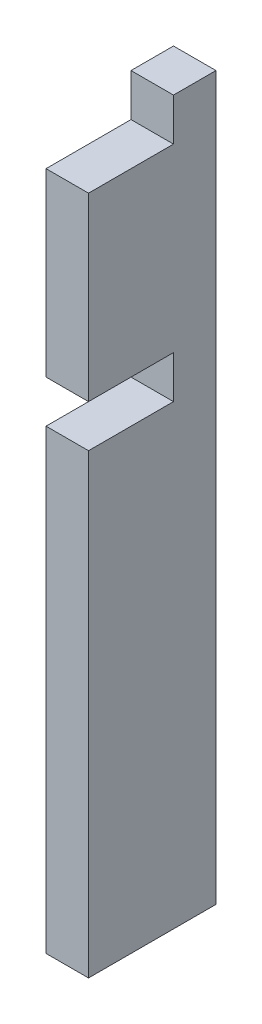
SolidWorks part; units mm, degrees
ref_plane "Front Plane" through (0, 0, 0) normal (0, 0, 1) x (1, 0, 0)
ref_plane "Top Plane" through (0, 0, 0) normal (0, 1, 0) x (1, 0, 0)
ref_plane "Right Plane" through (0, 0, 0) normal (1, 0, 0) x (0, 0, -1)
sketch "Sketch1" plane through (0, 0, 0) normal (1, 0, 0) x (0, 0, -1)
  line L1 (-9.525, 53.975) -> (9.525, 53.975)
  line L2 (-9.525, 53.975) -> (-9.525, -53.975)
  line L3 (-9.525, -53.975) -> (9.525, -53.975)
  line L4 (9.525, 53.975) -> (9.525, -53.975)
  line L5 (-9.525, 53.975) -> (9.525, -53.975) construction
  line L6 (-9.525, -53.975) -> (9.525, 53.975) construction
  point P0 (0, 0)
  dimension "D1" = 107.95
  dimension "D2" = 19.05
extrude "Boss-Extrude1" add sketch "Sketch1" along normal mid plane 6.35
sketch "Sketch2" plane through (3.175, 0, 0) normal (1, 0, 0) x (0, 0, -1)
  line L0 (-9.525, 53.975) -> (-9.525, -53.975) construction
  line L1 (-9.525, 53.975) -> (3.175, 53.975)
  line L2 (-9.525, 53.975) -> (-9.525, 47.625)
  line L3 (-9.525, 47.625) -> (3.175, 47.625)
  line L4 (3.175, 53.975) -> (3.175, 47.625)
  line L5 (-9.525, 20.6375) -> (3.175, 20.6375)
  line L6 (-9.525, 20.6375) -> (-9.525, 14.2875)
  line L7 (-9.525, 14.2875) -> (3.175, 14.2875)
  line L8 (3.175, 20.6375) -> (3.175, 14.2875)
  line L10 (-9.176, 20.6375) -> (53.9335, 20.6375) construction
  dimension "D1" = 6.35
  dimension "D2" = 12.7
  dimension "D5" = 6.35
extrude "Cut-Extrude1" cut sketch "Sketch2" against normal through all
